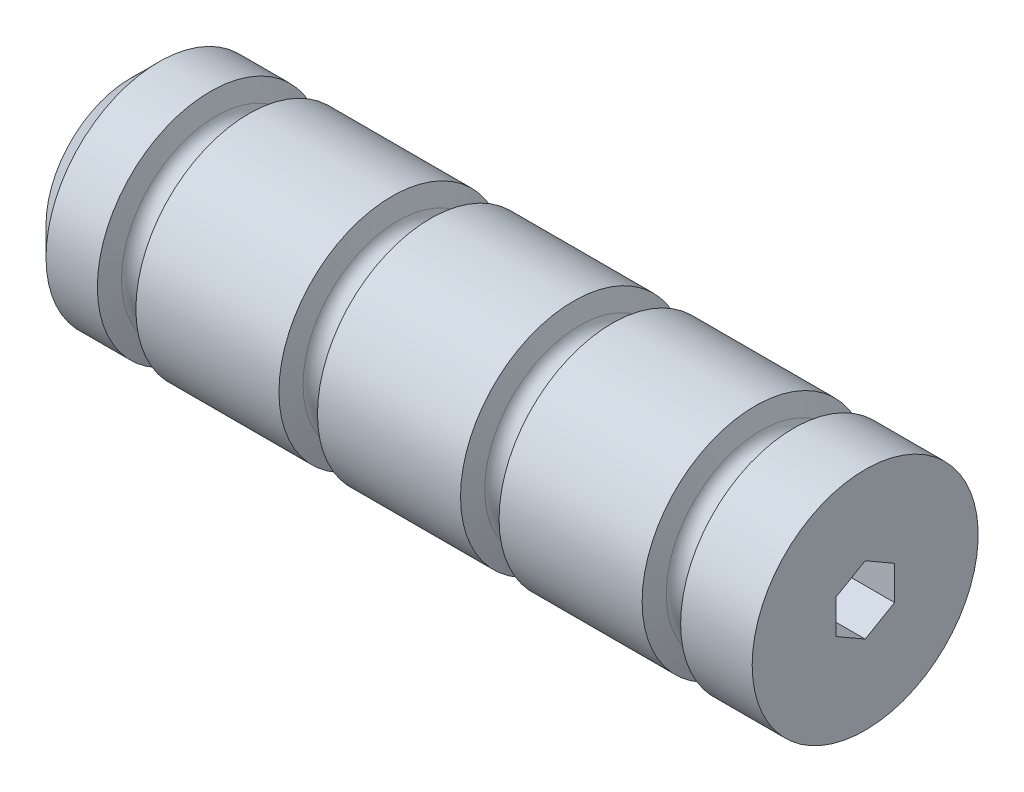
SolidWorks part; units mm, degrees
ref_plane "Front" through (0, 0, 0) normal (0, 0, 1) x (1, 0, 0)
ref_plane "Top" through (0, 0, 0) normal (0, 1, 0) x (1, 0, 0)
ref_plane "Right" through (0, 0, 0) normal (1, 0, 0) x (0, 0, -1)
sketch "Sketch1" plane through (0, 0, 0) normal (0, 0, 1) x (1, 0, 0)
  line L0 (0, 0) -> (0, 25.4)
  line L1 (0, 25.4) -> (-158.75, 25.4)
  line L2 (-165.1, 19.05) -> (-165.1, 0)
  line L3 (-165.1, 0) -> (0, 0)
  line L4 (0, 0) -> (30.4489, 0) construction
  line L5 (-158.75, 25.4) -> (-165.1, 19.05)
  point P4 (-165.1, 25.4)
  dimension "D1" = 165.1
  dimension "D2" = 50.8
revolve "Revolve1" add sketch "Sketch1" angle 360 about L4
sketch "Sketch2" plane through (0, 0, 0) normal (0, 0, 1) x (1, 0, 0)
  line L0 (-16.0806, 25.4) -> (-17.3827, 21.2703)
  line L1 (0, 25.4) -> (-158.75, 25.4) construction
  line L2 (-23.4388, 21.2703) -> (-24.7409, 25.4)
  line L3 (-24.7409, 25.4) -> (-16.0806, 25.4)
  line L4 (0, -25.4) -> (0, 25.4) construction
  line L5 (-56.902, 25.4) -> (-58.2041, 21.2703)
  line L6 (-64.2602, 21.2703) -> (-65.5623, 25.4)
  line L7 (-65.5623, 25.4) -> (-56.902, 25.4)
  line L8 (-97.7234, 25.4) -> (-99.0255, 21.2703)
  line L9 (-105.0816, 21.2703) -> (-106.3837, 25.4)
  line L10 (-106.3837, 25.4) -> (-97.7234, 25.4)
  line L11 (-138.5448, 25.4) -> (-139.8469, 21.2703)
  line L12 (-145.9031, 21.2703) -> (-147.2052, 25.4)
  line L13 (-147.2052, 25.4) -> (-138.5448, 25.4)
  line L14 (-165.1, 25.4) -> (-165.1, -25.4) construction
  line L15 (0, 0) -> (10.0769, 0) construction
  line L16 (-61.2321, 22.225) -> (-20.4107, 22.225) construction
  line L17 (-20.4107, 22.225) -> (20.4107, 22.225) construction
  arc A0 (-17.3827, 21.2703) -> (-23.4388, 21.2703) centre (-20.4107, 22.225) cw
  arc A1 (-58.2041, 21.2703) -> (-64.2602, 21.2703) centre (-61.2321, 22.225) cw
  arc A2 (-99.0255, 21.2703) -> (-105.0816, 21.2703) centre (-102.0536, 22.225) cw
  arc A3 (-139.8469, 21.2703) -> (-145.9031, 21.2703) centre (-142.875, 22.225) cw
  point P29 (0, 22.225)
  dimension "D2" = 3.175
  dimension "D3" = 6.35
  dimension "D6" = 22.225
  dimension "D1" = 35
  dimension "D5" = 4
revolve "Cut-Revolve1" cut sketch "Sketch2" angle 360 about L15
sketch "Sketch3" plane through (0, 0, 0) normal (1, 0, 0) x (0, 0, -1)
  line L1 (0, 7.6256) -> (-6.604, 3.8128)
  line L2 (-6.604, 3.8128) -> (-6.604, -3.8128)
  line L3 (-6.604, -3.8128) -> (0, -7.6256)
  line L4 (0, -7.6256) -> (6.604, -3.8128)
  line L5 (6.604, -3.8128) -> (6.604, 3.8128)
  line L6 (6.604, 3.8128) -> (0, 7.6256)
  circle A0 centre (0, 0) radius 6.604 construction
  dimension "D1" = 13.208
extrude "Cut-Extrude1" cut sketch "Sketch3" against normal through all
